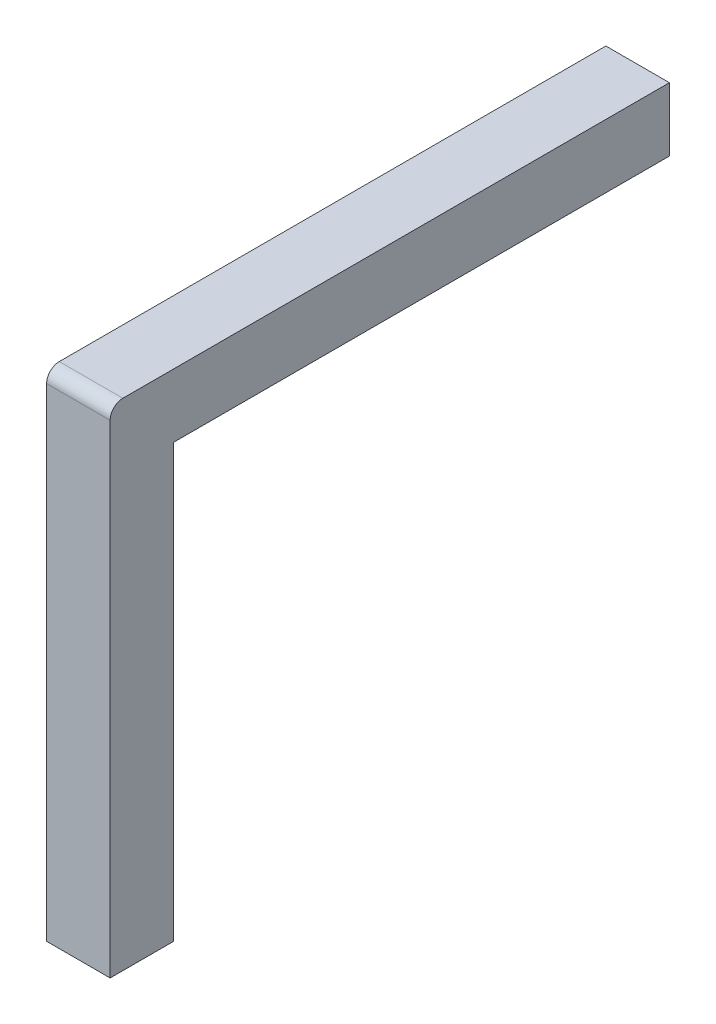
SolidWorks part; units mm, degrees
material "1060 Alloy"
ref_plane "Front Plane" through (0, 0, 0) normal (0, 0, 1) x (1, 0, 0)
ref_plane "Top Plane" through (0, 0, 0) normal (0, 1, 0) x (1, 0, 0)
ref_plane "Right Plane" through (0, 0, 0) normal (1, 0, 0) x (0, 0, -1)
sketch "Sketch2" plane through (0, 0, 0) normal (0, 1, 0) x (1, 0, 0)
  line L0 (-0.5, -0.5) -> (-0.5, 0.5)
  line L1 (-0.5, -0.5) -> (0.5, -0.5)
  line L2 (-0.5, 0.5) -> (0.5, 0.5)
  line L3 (0.5, -0.5) -> (0.5, 0.5)
  line L4 (-0.5, -0.5) -> (0.5, 0.5) construction
  line L5 (-0.5, 0.5) -> (0.5, -0.5) construction
  point P1 (0, 0)
  dimension "D1" = 1
extrude "Boss-Extrude1" add sketch "Sketch2" along normal blind 8
sketch "Sketch3" plane through (0, 0, -0.5) normal (0, 0, -1) x (-1, 0, 0)
  line L0 (-0.5, 8) -> (-0.5, 0) construction
  line L1 (0.5, 8) -> (-0.5, 8)
  line L2 (0.5, 8) -> (0.5, 7)
  line L3 (0.5, 7) -> (-0.5, 7)
  line L4 (-0.5, 8) -> (-0.5, 7)
  dimension "D1" = 1
extrude "Boss-Extrude2" add sketch "Sketch3" along normal blind 8
fillet "Fillet1" radius 0.2 1 edges at (0, 8, 0.5)
chamfer "Chamfer1" distance 0.2 angle 45 4 edges at (0.5, 7.5, -8.5) (0, 7, -8.5) (-0.5, 7.5, -8.5) (0, 8, -8.5)
chamfer "Chamfer2" distance 0.2 angle 45 4 edges at (0, 0, 0.5) (0.5, 0, 0) (0, 0, -0.5) (-0.5, 0, 0)
